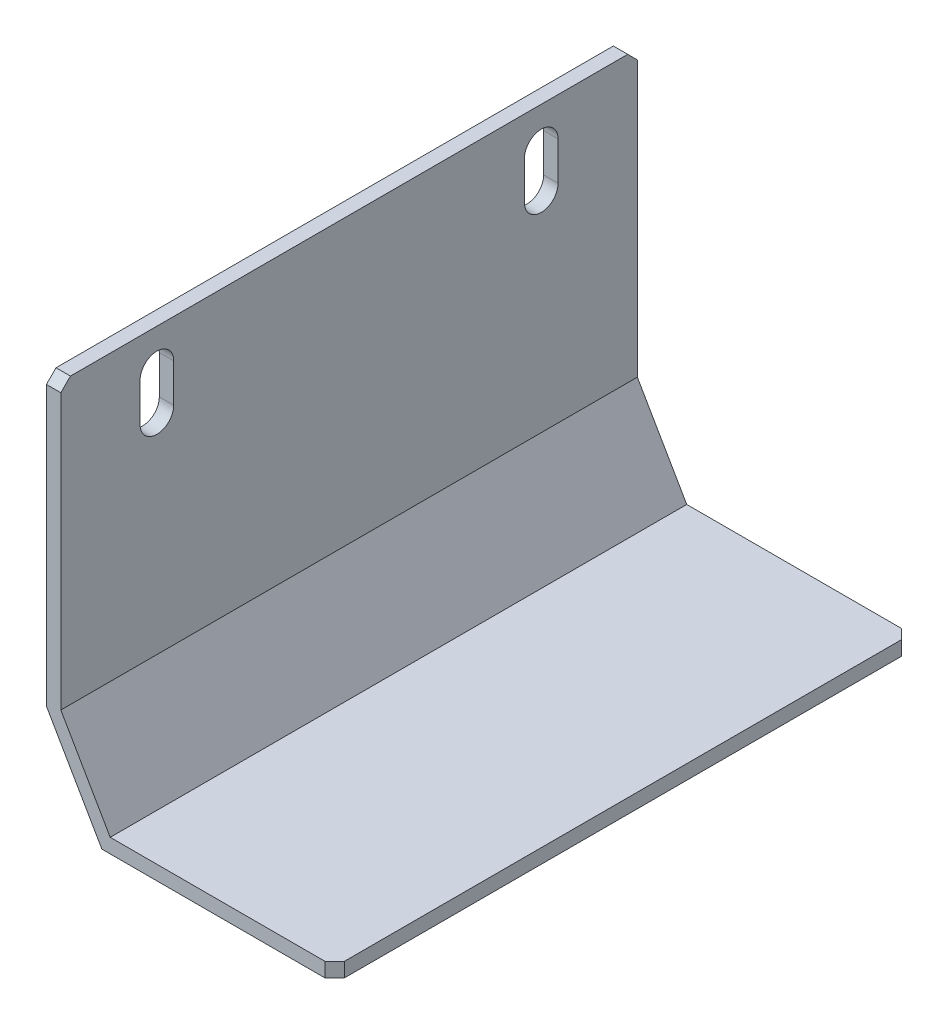
SolidWorks part; units mm, degrees
ref_plane "Front Plane" through (0, 0, 0) normal (0, 0, 1) x (1, 0, 0)
ref_plane "Top Plane" through (0, 0, 0) normal (0, 1, 0) x (1, 0, 0)
ref_plane "Right Plane" through (0, 0, 0) normal (1, 0, 0) x (0, 0, -1)
sketch "Sketch1" plane through (0, 0, 0) normal (0, 0, 1) x (1, 0, 0)
  line L0 (-13.3721, -14.2442) -> (-7.5986, -24.2442)
  line L1 (-13.3721, 15.7558) -> (-11.8721, 15.7558)
  line L2 (-13.3721, 15.7558) -> (-13.3721, -14.2442)
  line L3 (-11.8721, -13.8423) -> (-6.7326, -22.7442)
  line L4 (-11.8721, 15.7558) -> (-11.8721, -13.8423)
  line L5 (-6.7326, -22.7442) -> (16.6279, -22.7442)
  line L7 (-7.5986, -24.2442) -> (16.6279, -24.2442)
  line L8 (16.6279, -22.7442) -> (16.6279, -24.2442)
  dimension "D1" = 30
  dimension "D2" = 40
  dimension "D3" = 30
  dimension "D4" = 1.5
  dimension "D5" = 1.5
  dimension "D6" = 1.5
  dimension "D7" = 120
extrude "Boss-Extrude1" add sketch "Sketch1" along normal blind 60
sketch "Sketch3" plane through (-13.3721, 0, 0) normal (-1, 0, 0) x (0, 0, 1)
  line L2 (8.25, 11.7558) -> (8.25, 7.7558)
  line L4 (11.75, 11.7558) -> (11.75, 7.7558)
  line L6 (48.25, 11.7558) -> (48.25, 7.7558)
  line L8 (51.75, 11.7558) -> (51.75, 7.7558)
  arc A0 (11.75, 11.7558) -> (8.25, 11.7558) centre (10, 11.7558) ccw
  arc A1 (8.25, 7.7558) -> (11.75, 7.7558) centre (10, 7.7558) ccw
  arc A2 (48.25, 7.7558) -> (51.75, 7.7558) centre (50, 7.7558) ccw
  arc A3 (51.75, 11.7558) -> (48.25, 11.7558) centre (50, 11.7558) ccw
  dimension "D3" = 4
  dimension "D4" = 4
  dimension "D6" = 3.5
  dimension "D7" = 3.5
extrude "Cut-Extrude1" cut sketch "Sketch3" against normal blind 60
chamfer "Chamfer1" distance 1 angle 45 4 edges at (16.6279, -23.4942, 0) (16.6279, -23.4942, 60) (-12.6221, 15.7558, 60) (-12.6221, 15.7558, 0)
